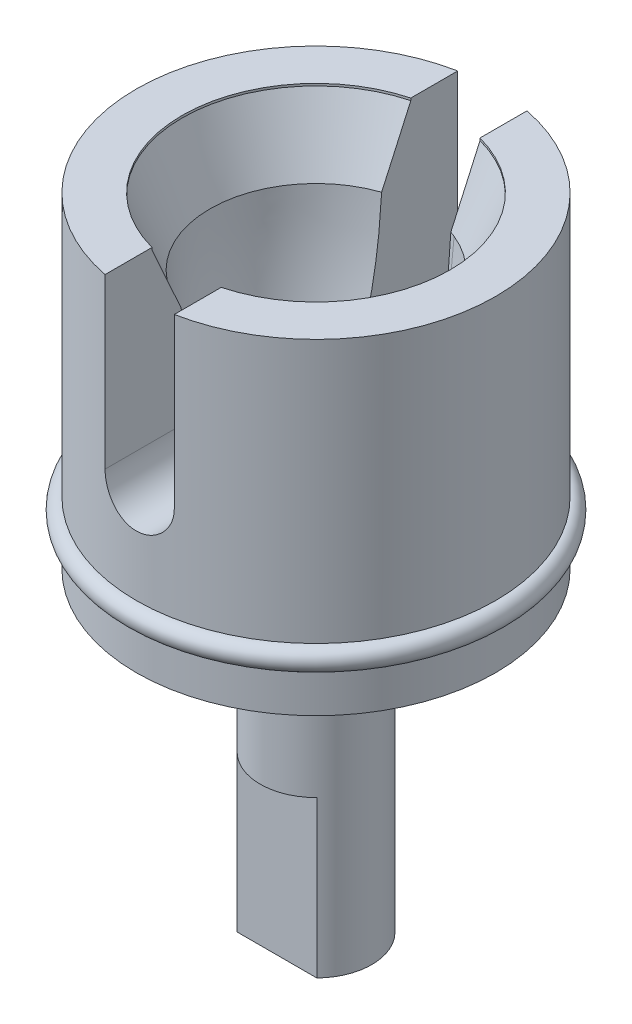
SolidWorks part; units mm, degrees
ref_plane "Front Plane" through (0, 0, 0) normal (0, 0, 1) x (1, 0, 0)
ref_plane "Top Plane" through (0, 0, 0) normal (0, 1, 0) x (1, 0, 0)
ref_plane "Right Plane" through (0, 0, 0) normal (1, 0, 0) x (0, 0, -1)
sketch "Sketch1" plane through (0, 0, 0) normal (0, 0, 1) x (1, 0, 0)
  line L0 (0, 0) -> (0, 33.8076) construction
  line L1 (6, 31.6804) -> (8.05, 31.6804)
  line L2 (8.05, 31.6804) -> (8.05, 19.8804)
  line L3 (8.05, 17.0804) -> (3.5, 17.0804)
  line L4 (0, 20.8804) -> (0.5, 20.8804)
  line L5 (8.05, 18.8804) -> (8.05, 17.0804)
  line L6 (0, 2.9804) -> (0, 20.8804)
  line L7 (0, 20.8804) -> (8.05, 20.8804) construction
  line L8 (2.5, 15.6804) -> (3.5, 15.6804)
  line L9 (3.5, 17.0804) -> (3.5, 15.6804)
  line L10 (0, 2.9804) -> (2.5, 2.9804)
  line L11 (2.5, 15.6804) -> (2.5, 2.9804)
  line L12 (6, 31.6804) -> (6, 31.5804)
  line L17 (4.75, 28.6804) -> (6, 31.5804)
  line L19 (0, 31.6804) -> (8.05, 31.6804) construction
  arc A0 (8.05, 18.8804) -> (8.05, 19.8804) centre (8.05, 19.3804) ccw
  spline S0 degree 3 poles (0.5, 20.8804) (0.9321, 20.9067) (1.8875, 20.9647) (3.5496, 21.8744) (4.2192, 24.3386) (4.6184, 26.6233) (4.718, 28.1808) (4.75, 28.6804) knots 0 0 0 0 0.130075 0.287608 0.531388 0.849689 1 1 1 1
  dimension "D2" = 14.6
  dimension "D3" = 3.5
  dimension "D4" = 1.4
  dimension "D5" = 2.5
  dimension "D6" = 28.7
  dimension "D8" = 0.1
  dimension "D9" = 6
  dimension "D7" = 10.8
revolve "Revolve1" add sketch "Sketch1" angle 360 about L0
sketch "Sketch2" plane through (0, 2.9804, 0) normal (0, -1, 0) x (1, 0, 0)
  line L0 (1.7854, 1.75) -> (4.2648, 1.75)
  line L1 (-4.47, 1.75) -> (1.7854, 1.75)
  line L2 (-4.47, 1.75) -> (0.4836, 4.6752)
  line L3 (-4.47, -1.75) -> (4.2648, -1.75)
  line L4 (0.4836, 4.6752) -> (4.2648, 1.75)
  line L5 (4.2648, -1.75) -> (0.3838, -4.0418)
  line L6 (0.3838, -4.0418) -> (-4.47, -1.75)
  dimension "D1" = 3.5
  dimension "D2" = 1.75
extrude "Extrude1" cut sketch "Sketch2" against normal blind 7
ref_plane "Plane1" through (0, 0, 10.75) normal (0, 0, 1) x (1, 0, 0)
sketch "Sketch3" plane through (0, 0, 10.75) normal (0, 0, 1) x (1, 0, 0)
  line L1 (-1.55, 37.6982) -> (1.55, 37.6982)
  line L2 (-1.55, 37.6982) -> (-1.55, 24.1304)
  line L3 (8.05, 31.6804) -> (-8.05, 31.6804) construction
  line L4 (1.55, 37.6982) -> (1.55, 24.1304)
  arc A0 (-1.55, 24.1304) -> (1.55, 24.1304) centre (0, 24.1304) ccw
  dimension "D4" = 3.1
  dimension "D3" = 7.55
  dimension "D1" = 3.1
  dimension "D2" = 1.55
extrude "Extrude2" cut sketch "Sketch3" against normal through all
